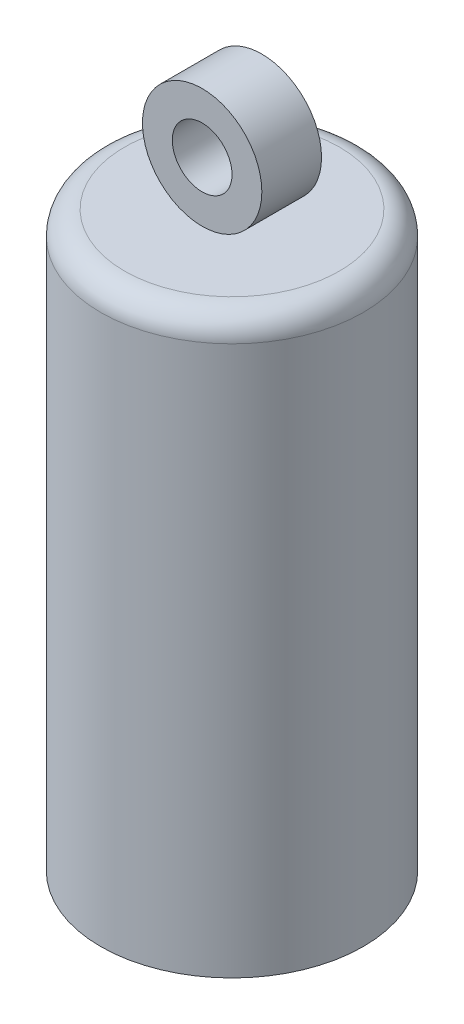
SolidWorks part; units mm, degrees
material "AISI 1010 Steel, hot rolled bar"
ref_plane "Front Plane" through (0, 0, 0) normal (0, 0, 1) x (1, 0, 0)
ref_plane "Top Plane" through (0, 0, 0) normal (0, 1, 0) x (1, 0, 0)
ref_plane "Right Plane" through (0, 0, 0) normal (1, 0, 0) x (0, 0, -1)
sketch "Sketch1" plane through (0, 0, 0) normal (0, 1, 0) x (1, 0, 0)
  circle A0 centre (0, 0) radius 5.5
  dimension "D1" = 11
extrude "Boss-Extrude1" add sketch "Sketch1" along normal blind 1.5
sketch "Sketch2" plane through (0, 0, 0) normal (0, 0, 1) x (1, 0, 0)
  line L0 (5.5, 1.5) -> (-5.5, 1.5) construction
  circle A0 centre (0, 4) radius 2.5
  circle A1 centre (0, 4) radius 1.25
  dimension "D1" = 5
  dimension "D3" = 2.5
  dimension "D2" = 2.5
extrude "Boss-Extrude2" add sketch "Sketch2" along normal mid plane 2.5 separate body
fillet "Fillet1" radius 1 1 edges at (0, 1.5, 5.5)
sketch "Sketch3" plane through (0, 0, 0) normal (0, -1, 0) x (1, 0, 0)
  circle A0 centre (0, 0) radius 5.5 construction
  circle A1 centre (0, 0) radius 5.5
  circle A2 centre (0, 0) radius 5.35
  dimension "D1" = 10.7
extrude "Boss-Extrude3" add sketch "Sketch3" along normal blind 22.5
sketch "Sketch4" plane through (0, 0, 0) normal (0, -1, 0) x (1, 0, 0)
  circle A0 centre (0, 0) radius 2.75
  circle A1 centre (0, 0) radius 2.6
  dimension "D1" = 5.5
  dimension "D2" = 5.2
extrude "Boss-Extrude4" add sketch "Sketch4" along normal blind 22.5
